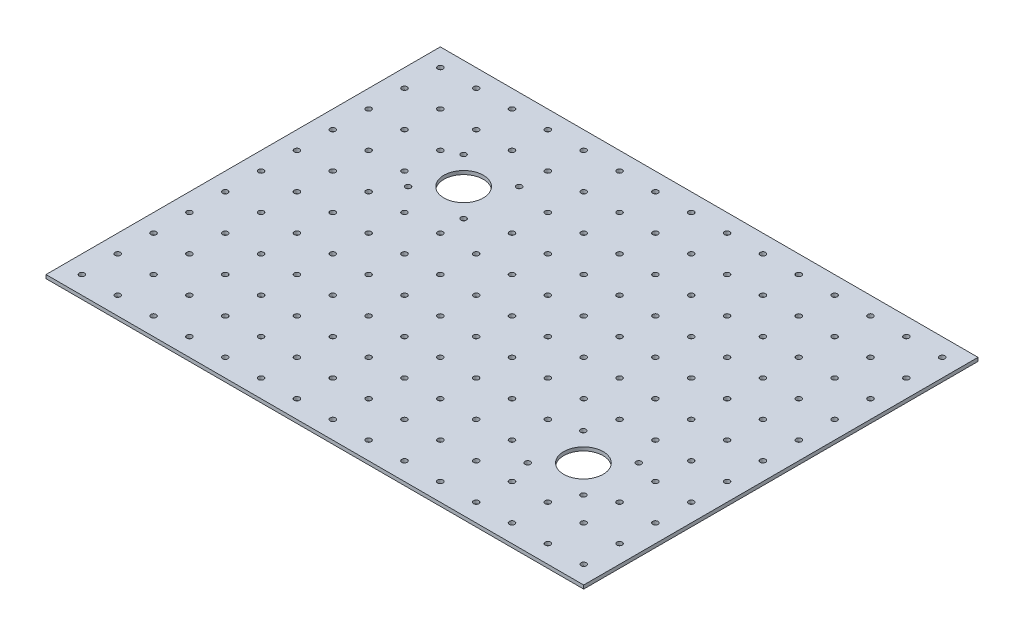
SolidWorks part; units mm, degrees
ref_plane "Front Plane" through (0, 0, 0) normal (0, 0, 1) x (1, 0, 0)
ref_plane "Top Plane" through (0, 0, 0) normal (0, 1, 0) x (1, 0, 0)
ref_plane "Right Plane" through (0, 0, 0) normal (1, 0, 0) x (0, 0, -1)
sketch "Sketch1" plane through (0, 0, 0) normal (1, 0, 0) x (0, 0, -1)
  line L0 (-26.6783, 0) -> (193.3217, 0)
  line L1 (55, 0) -> (-55, 0) construction
  line L2 (-26.6783, 0) -> (-26.6783, 2)
  line L3 (193.3217, 0) -> (193.3217, 2)
  line L4 (193.3217, 2) -> (-26.6783, 2)
  dimension "D1" = 220
  dimension "D2" = 2
extrude "Boss-Extrude1" add sketch "Sketch1" along normal blind 300 contours L4 L2 L0 L3
sketch "Sketch2" plane through (0, 2, 0) normal (0, 1, 0) x (1, 0, 0)
  line L0 (0, -55) -> (0, 55) construction
  line L7 (10, -6.6783) -> (11.5, -6.6783) construction
  line L18 (74, 132.3217) -> (85, 132.3217) construction
  line L20 (10, 3.3217) -> (11.5, 3.3217) construction
  line L24 (300, -26.6783) -> (0, -26.6783) construction
  line L27 (85, 132.3217) -> (63, 132.3217) construction
  line L52 (10, 23.3217) -> (11.5, 23.3217) construction
  line L62 (10, 63.3217) -> (11.5, 63.3217) construction
  line L82 (10, 143.3217) -> (11.5, 143.3217) construction
  line L84 (30, -16.6783) -> (30, -1.0997) construction
  circle A0 centre (74, 132.3217) radius 11
  circle A4 centre (89.5, 116.8217) radius 1.5
  circle A5 centre (58.5, 116.8217) radius 1.5
  circle A6 centre (89.5, 147.8217) radius 1.5
  circle A7 centre (58.5, 147.8217) radius 1.5
  circle A13 centre (256.3313, 47.7194) radius 1.5
  circle A14 centre (256.4575, 16.7194) radius 1.5
  circle A15 centre (225.3313, 16.7194) radius 1.5
  circle A16 centre (225.3313, 47.7194) radius 1.5
  circle A17 centre (240.9575, 32.2194) radius 11
  circle A23 centre (10, -16.6783) radius 1.5
  circle A26 centre (10, 3.3217) radius 1.5
  circle A27 centre (10, 23.3217) radius 1.5
  circle A29 centre (10, 63.3217) radius 1.5
  circle A31 centre (10, 43.3217) radius 1.5
  circle A33 centre (10, 143.3217) radius 1.5
  circle A35 centre (10, 123.3217) radius 1.5
  circle A37 centre (10, 103.3217) radius 1.5
  circle A39 centre (10, 83.3217) radius 1.5
  circle A45 centre (10, 183.3217) radius 1.5
  circle A47 centre (10, 163.3217) radius 1.5
  circle A49 centre (30, -16.6783) radius 1.5
  circle A50 centre (30, 3.3217) radius 1.5
  circle A51 centre (30, 23.3217) radius 1.5
  circle A52 centre (30, 43.3217) radius 1.5
  circle A53 centre (30, 63.3217) radius 1.5
  circle A54 centre (30, 83.3217) radius 1.5
  circle A55 centre (30, 103.3217) radius 1.5
  circle A56 centre (30, 123.3217) radius 1.5
  circle A57 centre (30, 143.3217) radius 1.5
  circle A58 centre (30, 163.3217) radius 1.5
  circle A59 centre (30, 183.3217) radius 1.5
  circle A60 centre (50, -16.6783) radius 1.5
  circle A61 centre (50, 3.3217) radius 1.5
  circle A62 centre (50, 23.3217) radius 1.5
  circle A63 centre (50, 43.3217) radius 1.5
  circle A64 centre (50, 63.3217) radius 1.5
  circle A65 centre (50, 83.3217) radius 1.5
  circle A66 centre (50, 103.3217) radius 1.5
  circle A67 centre (50, 123.3217) radius 1.5
  circle A68 centre (50, 143.3217) radius 1.5
  circle A69 centre (50, 163.3217) radius 1.5
  circle A70 centre (50, 183.3217) radius 1.5
  circle A71 centre (70, -16.6783) radius 1.5
  circle A72 centre (70, 3.3217) radius 1.5
  circle A73 centre (70, 23.3217) radius 1.5
  circle A74 centre (70, 43.3217) radius 1.5
  circle A75 centre (70, 63.3217) radius 1.5
  circle A76 centre (70, 83.3217) radius 1.5
  circle A77 centre (70, 103.3217) radius 1.5
  circle A80 centre (70, 163.3217) radius 1.5
  circle A81 centre (70, 183.3217) radius 1.5
  circle A82 centre (90, -16.6783) radius 1.5
  circle A83 centre (90, 3.3217) radius 1.5
  circle A84 centre (90, 23.3217) radius 1.5
  circle A85 centre (90, 43.3217) radius 1.5
  circle A86 centre (90, 63.3217) radius 1.5
  circle A87 centre (90, 83.3217) radius 1.5
  circle A88 centre (90, 103.3217) radius 1.5
  circle A91 centre (90, 163.3217) radius 1.5
  circle A92 centre (90, 183.3217) radius 1.5
  circle A93 centre (110, -16.6783) radius 1.5
  circle A94 centre (110, 3.3217) radius 1.5
  circle A95 centre (110, 23.3217) radius 1.5
  circle A96 centre (110, 43.3217) radius 1.5
  circle A97 centre (110, 63.3217) radius 1.5
  circle A98 centre (110, 83.3217) radius 1.5
  circle A99 centre (110, 103.3217) radius 1.5
  circle A100 centre (110, 123.3217) radius 1.5
  circle A101 centre (110, 143.3217) radius 1.5
  circle A102 centre (110, 163.3217) radius 1.5
  circle A103 centre (110, 183.3217) radius 1.5
  circle A104 centre (130, -16.6783) radius 1.5
  circle A105 centre (130, 3.3217) radius 1.5
  circle A106 centre (130, 23.3217) radius 1.5
  circle A107 centre (130, 43.3217) radius 1.5
  circle A108 centre (130, 63.3217) radius 1.5
  circle A109 centre (130, 83.3217) radius 1.5
  circle A110 centre (130, 103.3217) radius 1.5
  circle A111 centre (130, 123.3217) radius 1.5
  circle A112 centre (130, 143.3217) radius 1.5
  circle A113 centre (130, 163.3217) radius 1.5
  circle A114 centre (130, 183.3217) radius 1.5
  circle A115 centre (150, -16.6783) radius 1.5
  circle A116 centre (150, 3.3217) radius 1.5
  circle A117 centre (150, 23.3217) radius 1.5
  circle A118 centre (150, 43.3217) radius 1.5
  circle A119 centre (150, 63.3217) radius 1.5
  circle A120 centre (150, 83.3217) radius 1.5
  circle A121 centre (150, 103.3217) radius 1.5
  circle A122 centre (150, 123.3217) radius 1.5
  circle A123 centre (150, 143.3217) radius 1.5
  circle A124 centre (150, 163.3217) radius 1.5
  circle A125 centre (150, 183.3217) radius 1.5
  circle A126 centre (170, -16.6783) radius 1.5
  circle A127 centre (170, 3.3217) radius 1.5
  circle A128 centre (170, 23.3217) radius 1.5
  circle A129 centre (170, 43.3217) radius 1.5
  circle A130 centre (170, 63.3217) radius 1.5
  circle A131 centre (170, 83.3217) radius 1.5
  circle A132 centre (170, 103.3217) radius 1.5
  circle A133 centre (170, 123.3217) radius 1.5
  circle A134 centre (170, 143.3217) radius 1.5
  circle A135 centre (170, 163.3217) radius 1.5
  circle A136 centre (170, 183.3217) radius 1.5
  circle A137 centre (190, -16.6783) radius 1.5
  circle A138 centre (190, 3.3217) radius 1.5
  circle A139 centre (190, 23.3217) radius 1.5
  circle A140 centre (190, 43.3217) radius 1.5
  circle A141 centre (190, 63.3217) radius 1.5
  circle A142 centre (190, 83.3217) radius 1.5
  circle A143 centre (190, 103.3217) radius 1.5
  circle A144 centre (190, 123.3217) radius 1.5
  circle A145 centre (190, 143.3217) radius 1.5
  circle A146 centre (190, 163.3217) radius 1.5
  circle A147 centre (190, 183.3217) radius 1.5
  circle A148 centre (210, -16.6783) radius 1.5
  circle A149 centre (210, 3.3217) radius 1.5
  circle A150 centre (210, 23.3217) radius 1.5
  circle A151 centre (210, 43.3217) radius 1.5
  circle A152 centre (210, 63.3217) radius 1.5
  circle A153 centre (210, 83.3217) radius 1.5
  circle A154 centre (210, 103.3217) radius 1.5
  circle A155 centre (210, 123.3217) radius 1.5
  circle A156 centre (210, 143.3217) radius 1.5
  circle A157 centre (210, 163.3217) radius 1.5
  circle A158 centre (210, 183.3217) radius 1.5
  circle A159 centre (230, -16.6783) radius 1.5
  circle A160 centre (230, 3.3217) radius 1.5
  circle A163 centre (230, 63.3217) radius 1.5
  circle A164 centre (230, 83.3217) radius 1.5
  circle A165 centre (230, 103.3217) radius 1.5
  circle A166 centre (230, 123.3217) radius 1.5
  circle A167 centre (230, 143.3217) radius 1.5
  circle A168 centre (230, 163.3217) radius 1.5
  circle A169 centre (230, 183.3217) radius 1.5
  circle A170 centre (250, -16.6783) radius 1.5
  circle A171 centre (250, 3.3217) radius 1.5
  circle A174 centre (250, 63.3217) radius 1.5
  circle A175 centre (250, 83.3217) radius 1.5
  circle A176 centre (250, 103.3217) radius 1.5
  circle A177 centre (250, 123.3217) radius 1.5
  circle A178 centre (250, 143.3217) radius 1.5
  circle A179 centre (250, 163.3217) radius 1.5
  circle A180 centre (250, 183.3217) radius 1.5
  circle A181 centre (270, -16.6783) radius 1.5
  circle A182 centre (270, 3.3217) radius 1.5
  circle A183 centre (270, 23.3217) radius 1.5
  circle A184 centre (270, 43.3217) radius 1.5
  circle A185 centre (270, 63.3217) radius 1.5
  circle A186 centre (270, 83.3217) radius 1.5
  circle A187 centre (270, 103.3217) radius 1.5
  circle A188 centre (270, 123.3217) radius 1.5
  circle A189 centre (270, 143.3217) radius 1.5
  circle A190 centre (270, 163.3217) radius 1.5
  circle A191 centre (270, 183.3217) radius 1.5
  circle A192 centre (290, -16.6783) radius 1.5
  circle A193 centre (290, 3.3217) radius 1.5
  circle A194 centre (290, 23.3217) radius 1.5
  circle A195 centre (290, 43.3217) radius 1.5
  circle A196 centre (290, 63.3217) radius 1.5
  circle A197 centre (290, 83.3217) radius 1.5
  circle A198 centre (290, 103.3217) radius 1.5
  circle A199 centre (290, 123.3217) radius 1.5
  circle A200 centre (290, 143.3217) radius 1.5
  circle A201 centre (290, 163.3217) radius 1.5
  circle A202 centre (290, 183.3217) radius 1.5
  circle A203 centre (230, 43.3217) radius 1.5 [skipped]
  circle A204 centre (230, 23.3217) radius 1.5 [skipped]
  circle A205 centre (250, 23.3217) radius 1.5 [skipped]
  circle A206 centre (250, 43.3217) radius 1.5 [skipped]
  arc A207 (71.4708, 143.027) -> (69.0621, 142.1511) centre (70, 143.3217) cw [skipped]
  arc A208 (68.6238, 122.725) -> (70.4793, 121.9003) centre (70, 123.3217) ccw [skipped]
  circle A209 centre (90, 123.3217) radius 1.5 [skipped]
  circle A210 centre (90, 143.3217) radius 1.5 [skipped]
  dimension "D9" = 22
  dimension "D10" = 3
  dimension "D11" = 3
  dimension "D38" = 3
  dimension "D4" = 15
  dimension "D2" = 10
  dimension "D5" = 10
  dimension "D6" = 20
  dimension "D8" = 31
  dimension "D12" = 31
  dimension "D13" = 15.5
  dimension "D14" = 15.5
  dimension "D39" = 10
extrude "Cut-Extrude1" cut sketch "Sketch2" against normal blind 10
